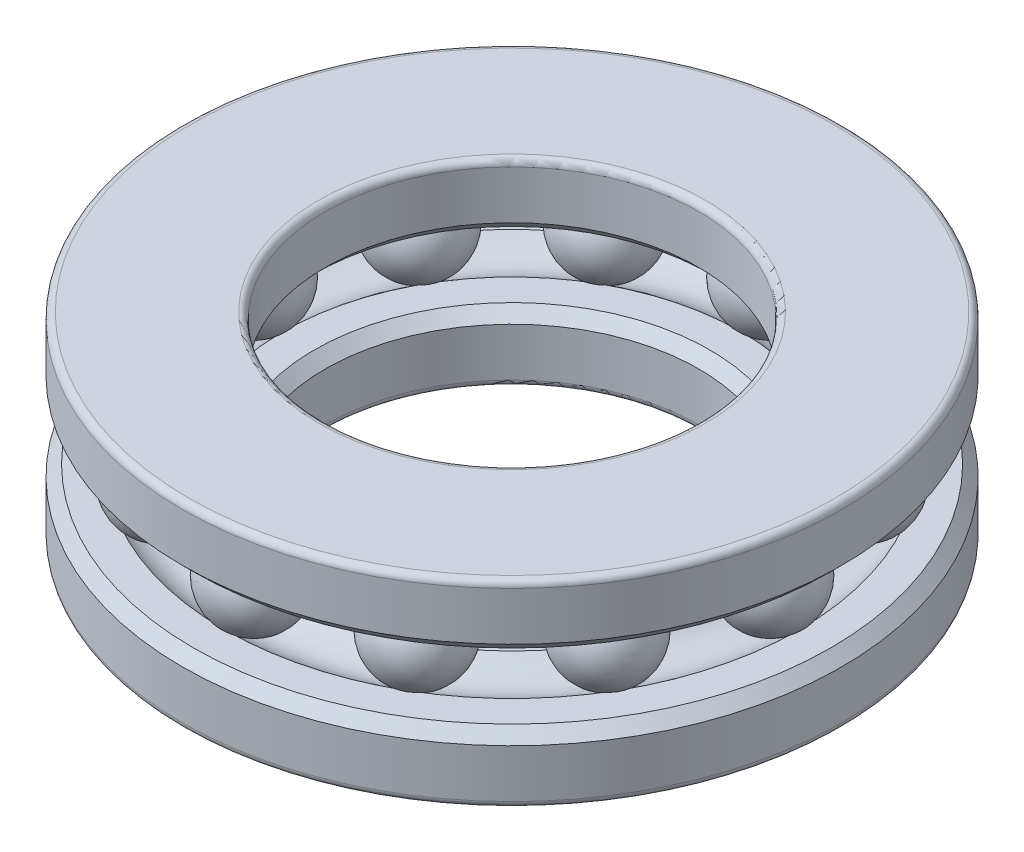
SolidWorks part; units mm, degrees
ref_plane "Front Plane" through (0, 0, 0) normal (0, 0, 1) x (1, 0, 0)
ref_plane "Top Plane" through (0, 0, 0) normal (0, 1, 0) x (1, 0, 0)
ref_plane "Right Plane" through (0, 0, 0) normal (1, 0, 0) x (0, 0, -1)
sketch "Sketch1" plane through (0, 0, 0) normal (1, 0, 0) x (0, 0, -1)
  line L0 (0, 0) -> (-15.8571, 0) construction
  line L1 (-11.75, 0) -> (-11.75, 5.4857) construction
  line L2 (-11.75, 0) -> (-11.75, -4.4857) construction
  line L3 (0, 0) -> (0, 10.4429) construction
  line L4 (-15, -4.5) -> (-8.5, -4.5)
  line L5 (-15, -4.5) -> (-15, -1.5)
  line L6 (-15, -1.5) -> (-8.5, -1.5)
  line L7 (-8.5, -4.5) -> (-8.5, -1.5)
  line L8 (-15, -4.5) -> (-8.5, -1.5) construction
  line L9 (-15, -1.5) -> (-8.5, -4.5) construction
  line L10 (-15, 4.5) -> (-8.5, 4.5)
  line L11 (-15, 4.5) -> (-15, 1.5)
  line L12 (-15, 1.5) -> (-8.5, 1.5)
  line L13 (-8.5, 4.5) -> (-8.5, 1.5)
  line L14 (-15, 4.5) -> (-8.5, 1.5) construction
  line L15 (-15, 1.5) -> (-8.5, 4.5) construction
  line L16 (-8.5, 1.5) -> (-8.5, -1.5) construction
  circle A0 centre (-11.75, 0) radius 2
  point P6 (-11.75, -3)
  point P12 (-11.75, 3)
  point P18 (-8.5, 0)
  dimension "D1" = 30
  dimension "D4" = 4
  dimension "D2" = 17
  dimension "D3" = 9
  dimension "D5" = 3
revolve "Revolve1" add sketch "Sketch1" angle 360 about L3
fillet "Fillet1" radius 0.3 2 edges at (0, 4.5, -8.5) (0, 4.5, -15)
fillet "Fillet2" radius 0.3 2 edges at (0, -4.5, -15) (0, -4.5, -8.5)
chamfer "Chamfer1" distance 0.5 angle 45 2 edges at (0, 1.5, -8.5) (0, 1.5, -15)
chamfer "Chamfer2" distance 0.5 angle 45 2 edges at (0, -1.5, -8.5) (0, -1.5, -15)
sketch "Sketch3" plane through (0, 0, 0) normal (1, 0, 0) x (0, 0, -1)
  line L0 (-11.75, 0) -> (-11.75, 6.8639) construction
  line L1 (-11.75, 6.8639) -> (-11.75, 9.8299) construction
  line L2 (-11.75, 2.05) -> (-11.75, -2.05)
  line L4 (-15, -4.5) -> (-8.5, -4.5)
  line L5 (-8.5, -4.5) -> (-8.5, -1.5)
  line L6 (-8.5, -1.5) -> (-15, -1.5)
  line L7 (-15, -1.5) -> (-15, -4.5)
  line L8 (-15, -4.5) -> (-8.5, -4.5) construction
  line L9 (-8.5, -4.5) -> (-8.5, -1.5) construction
  line L10 (-8.5, -1.5) -> (-15, -1.5) construction
  line L11 (-15, -1.5) -> (-15, -4.5) construction
  line L12 (-8.5, 4.5) -> (-15, 4.5)
  line L13 (-15, 4.5) -> (-15, 1.5)
  line L14 (-15, 1.5) -> (-8.5, 1.5)
  line L15 (-8.5, 1.5) -> (-8.5, 4.5)
  line L16 (-8.5, 4.5) -> (-15, 4.5) construction
  line L17 (-15, 4.5) -> (-15, 1.5) construction
  line L18 (-15, 1.5) -> (-8.5, 1.5) construction
  line L19 (-8.5, 1.5) -> (-8.5, 4.5) construction
  arc A0 (-11.75, -2.05) -> (-11.75, 2.05) centre (-11.75, 0) ccw
  circle A1 centre (-11.75, 0) radius 2
  circle A2 centre (-11.75, 0) radius 2 construction
  circle A3 centre (-11.75, 0) radius 2.05 construction
  dimension "D1" = 0
  dimension "D2" = 0
  dimension "D3" = 0
  dimension "D4" = 0.05
revolve "Revolve12" add sketch "Sketch3" angle 360 about L0
pattern_circular "CirPattern1" count 12 over 360 about axis through (0, 0, 0) along (0, 1, 0) of bodies 103
